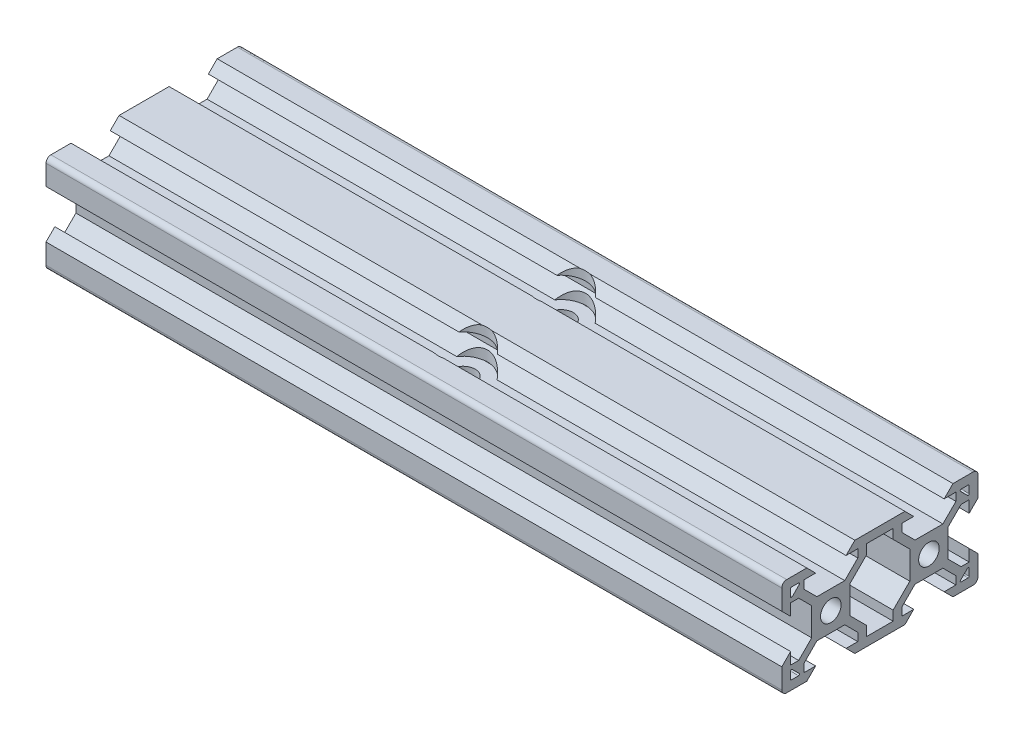
SolidWorks part; units mm, degrees
material "1060 Alloy"
ref_plane "Front Plane" through (0, 0, 0) normal (0, 0, 1) x (1, 0, 0)
ref_plane "Top Plane" through (0, 0, 0) normal (0, 1, 0) x (1, 0, 0)
ref_plane "Right Plane" through (0, 0, 0) normal (1, 0, 0) x (0, 0, -1)
sketch "Sketch4" plane through (0, 0, 0) normal (1, 0, 0) x (0, 0, -1)
  line L0 (-19.2399, 7.0114) -> (20.7601, 7.0114) construction
  dimension "D1" = 40
sketch "Sketch5" plane through (0, 0, 0) normal (1, 0, 0) x (0, 0, -1)
  line L0 (-19.998, 4.9) -> (-18.198, 3.1)
  line L1 (-18.198, 3.1) -> (-18.198, 5.4993)
  line L2 (-18.198, 5.4993) -> (-16.558, 5.4993)
  line L3 (-16.558, 5.4993) -> (-13.9, 2.8413)
  line L4 (-13.9, 2.8413) -> (-13.9, -2.8387)
  line L5 (-13.9, -2.8387) -> (-16.558, -5.4967)
  line L6 (-16.558, -5.4967) -> (-18.198, -5.4967)
  line L7 (-18.198, -5.4967) -> (-18.198, -3.1)
  line L8 (-18.198, -3.1) -> (-19.998, -4.9)
  line L9 (-19.998, -4.9) -> (-19.998, -9)
  line L10 (-18.998, -10) -> (-14.9, -10)
  line L11 (-14.9, -10) -> (-13.1, -8.2)
  line L12 (-13.1, -8.2) -> (-15.5, -8.2)
  line L13 (-15.5, -8.2) -> (-15.5, -6.56)
  line L14 (-15.5, -6.56) -> (-12.84, -3.9)
  line L15 (-12.84, -3.9) -> (-7.16, -3.9)
  line L16 (-7.16, -3.9) -> (-4.5, -6.56)
  line L17 (-4.5, -6.56) -> (-4.5, -8.2)
  line L18 (-4.5, -8.2) -> (-6.9, -8.2)
  line L19 (-6.9, -8.2) -> (-5.1, -10)
  line L20 (-5.1, -10) -> (5.1, -10)
  line L21 (5.1, -10) -> (6.9, -8.2)
  line L22 (6.9, -8.2) -> (4.496, -8.2)
  line L23 (4.496, -8.2) -> (4.496, -6.56)
  line L24 (4.496, -6.56) -> (7.156, -3.9)
  line L25 (7.156, -3.9) -> (12.836, -3.9)
  line L26 (12.836, -3.9) -> (15.496, -6.56)
  line L27 (15.496, -6.56) -> (15.496, -8.2)
  line L28 (15.496, -8.2) -> (13.1, -8.2)
  line L29 (13.1, -8.2) -> (14.9, -10)
  line L30 (14.9, -10) -> (19.002, -10)
  line L31 (20.002, -9) -> (20.002, -4.9)
  line L32 (20.002, -4.9) -> (18.202, -3.1)
  line L33 (18.202, -3.1) -> (18.202, -5.5046)
  line L34 (18.202, -5.5046) -> (16.562, -5.5046)
  line L35 (16.562, -5.5046) -> (13.9, -2.8426)
  line L36 (13.9, -2.8426) -> (13.9, 2.8374)
  line L37 (13.9, 2.8374) -> (16.562, 5.4993)
  line L38 (16.562, 5.4993) -> (18.202, 5.4993)
  line L39 (18.202, 5.4993) -> (18.202, 3.1)
  line L40 (18.202, 3.1) -> (20.002, 4.9)
  line L41 (20.002, 4.9) -> (20.002, 9)
  line L42 (19.002, 10) -> (14.9, 10)
  line L43 (14.9, 10) -> (13.1, 8.2)
  line L44 (13.1, 8.2) -> (15.5013, 8.2)
  line L45 (15.5013, 8.2) -> (15.5013, 6.56)
  line L46 (15.5013, 6.56) -> (12.8413, 3.9)
  line L47 (12.8413, 3.9) -> (7.1613, 3.9)
  line L48 (7.1613, 3.9) -> (4.5013, 6.56)
  line L49 (4.5013, 6.56) -> (4.5013, 8.2)
  line L50 (4.5013, 8.2) -> (6.9, 8.2)
  line L51 (6.9, 8.2) -> (5.1, 10)
  line L52 (5.1, 10) -> (-5.1, 10)
  line L53 (-5.1, 10) -> (-6.9, 8.2)
  line L54 (-6.9, 8.2) -> (-4.5013, 8.2)
  line L55 (-4.5013, 8.2) -> (-4.5013, 6.56)
  line L56 (-4.5013, 6.56) -> (-7.1613, 3.9)
  line L57 (-7.1613, 3.9) -> (-12.8413, 3.9)
  line L58 (-12.8413, 3.9) -> (-15.5013, 6.56)
  line L59 (-15.5013, 6.56) -> (-15.5013, 8.2)
  line L60 (-15.5013, 8.2) -> (-13.1, 8.2)
  line L61 (-13.1, 8.2) -> (-14.9, 10)
  line L62 (-14.9, 10) -> (-18.998, 10)
  line L63 (-19.998, 9) -> (-19.998, 4.9)
  line L64 (6.1, -2.84) -> (6.1, 2.84)
  line L65 (6.1, 2.84) -> (2.7, 6.24)
  line L66 (2.7, 6.24) -> (2.7, 8.2)
  line L67 (2.7, 8.2) -> (-2.7, 8.2)
  line L68 (-2.7, 8.2) -> (-2.7, 6.24)
  line L69 (-2.7, 6.24) -> (-6.1, 2.84)
  line L70 (-6.1, 2.84) -> (-6.1, -2.84)
  line L71 (-6.1, -2.84) -> (-2.7, -6.24)
  line L72 (-2.7, -6.24) -> (-2.7, -8.2)
  line L73 (-2.7, -8.2) -> (2.7, -8.2)
  line L74 (2.7, -8.2) -> (2.7, -6.24)
  line L75 (2.7, -6.24) -> (6.1, -2.84)
  line L76 (0, -8.2) -> (0, 8.2) construction
  line L77 (6.1, 0) -> (-6.1, 0) construction
  line L78 (16.562, 5.4993) -> (15.5013, 6.56) construction
  line L79 (16.5713, 8.2) -> (18.002, 8.2)
  line L81 (17.8606, 6.4279) -> (16.4299, 7.8586)
  line L82 (18.202, 8) -> (18.202, 6.5693)
  line L83 (18.002, 6.5693) -> (18.002, 8) construction
  line L84 (18.002, 8) -> (16.5713, 8) construction
  line L85 (16.5713, 8) -> (18.002, 6.5693) construction
  line L86 (16.5713, -8.2) -> (18.002, -8.2)
  line L87 (18.202, -8) -> (18.202, -6.5693)
  line L88 (17.8606, -6.4279) -> (16.4299, -7.8586)
  line L89 (-17.8606, 6.4279) -> (-16.4299, 7.8586)
  line L90 (-16.5713, 8.2) -> (-18.002, 8.2)
  line L91 (-18.202, 8) -> (-18.202, 6.5693)
  line L92 (-16.5713, -8.2) -> (-18.002, -8.2)
  line L93 (-17.8606, -6.4279) -> (-16.4299, -7.8586)
  line L94 (-18.202, -8) -> (-18.202, -6.5693)
  circle A0 centre (-10, 0) radius 2.1
  circle A1 centre (10, 0) radius 2.1
  arc A2 (-19.998, -9) -> (-18.998, -10) centre (-18.998, -9) ccw
  arc A5 (-18.998, 10) -> (-19.998, 9) centre (-18.998, 9) ccw
  arc A6 (20.002, -9) -> (19.002, -10) centre (19.002, -9) cw
  arc A7 (20.002, 9) -> (19.002, 10) centre (19.002, 9) ccw
  arc A8 (18.002, 8.2) -> (18.202, 8) centre (18.002, 8) cw
  arc A10 (16.4299, 7.8586) -> (16.5713, 8.2) centre (16.5713, 8) cw
  arc A12 (18.202, 6.5693) -> (17.8606, 6.4279) centre (18.002, 6.5693) cw
  arc A13 (16.4299, -7.8586) -> (16.5713, -8.2) centre (16.5713, -8) ccw
  arc A14 (18.002, -8.2) -> (18.202, -8) centre (18.002, -8) ccw
  arc A15 (18.202, -6.5693) -> (17.8606, -6.4279) centre (18.002, -6.5693) ccw
  arc A16 (-18.202, 6.5693) -> (-17.8606, 6.4279) centre (-18.002, 6.5693) ccw
  arc A17 (-16.4299, 7.8586) -> (-16.5713, 8.2) centre (-16.5713, 8) ccw
  arc A18 (-18.002, 8.2) -> (-18.202, 8) centre (-18.002, 8) ccw
  arc A19 (-18.002, -8.2) -> (-18.202, -8) centre (-18.002, -8) cw
  arc A20 (-16.4299, -7.8586) -> (-16.5713, -8.2) centre (-16.5713, -8) cw
  arc A21 (-18.202, -6.5693) -> (-17.8606, -6.4279) centre (-18.002, -6.5693) cw
  dimension "D1" = 4.2
  dimension "D20" = 3.9
  dimension "D27" = 1
  dimension "D40" = 1
  dimension "D41" = 1
  dimension "D42" = 1
  dimension "D45" = 0.2
  dimension "D47" = 1.07
  dimension "D48" = 1.07
  dimension "D49" = 0.2
  dimension "D2" = 20
  dimension "D3" = 10
  dimension "D4" = 5.68
  dimension "D5" = 5.4
  dimension "D6" = 1.96
  dimension "D7" = 45
  dimension "D8" = 1.8
  dimension "D9" = 1.64
  dimension "D10" = 1.8
  dimension "D11" = 40
  dimension "D12" = 20
  dimension "D13" = 3.9
  dimension "D14" = 1.5
  dimension "D15" = 1.5
  dimension "D16" = 3.9
  dimension "D17" = 3.9
  dimension "D18" = 3.9
  dimension "D19" = 3.9
  dimension "D21" = 1.5
  dimension "D22" = 1.5
  dimension "D23" = 1.64
  dimension "D24" = 45
  dimension "D25" = 1.5
  dimension "D26" = 1.8
  dimension "D28" = 6.2
  dimension "D29" = 6.2
  dimension "D30" = 6.2
  dimension "D31" = 6.2
  dimension "D32" = 6.2
  dimension "D33" = 3.1
  dimension "D34" = 3.1
  dimension "D35" = 3.1
  dimension "D36" = 3.1
  dimension "D37" = 6.2
  dimension "D38" = 3.1
  dimension "D39" = 3.1
  dimension "D43" = 1.64
  dimension "D44" = 135
  dimension "D46" = 45
extrude "Boss-Extrude1" add sketch "Sketch5" along normal mid plane 150
sketch "Sketch6" plane through (0, 10, 0) normal (0, 1, 0) x (1, 0, 0)
  line L0 (75, 10.0013) -> (-75, 10.0013) construction
  line L3 (75, 12.8413) -> (75, 7.1613) construction
  line L4 (-75, 12.8413) -> (-75, 7.1613) construction
  line L5 (0, 10.0013) -> (0, -18.998) construction
  line L6 (75, -18.998) -> (-75, -18.998) construction
  line L7 (-75, 0) -> (75, 0) construction
  line L8 (-75, 5.1) -> (-75, -5.1) construction
  line L9 (75, 5.1) -> (75, -5.1) construction
  circle A0 centre (0, 10.0013) radius 2.5
  circle A1 centre (0, -10.0013) radius 2.5
  dimension "D1" = 5
extrude "Cut-Extrude1" cut sketch "Sketch6" against normal up to next
sketch "Sketch7" plane through (0, 10, 0) normal (0, 1, 0) x (1, 0, 0)
  line L0 (-75, 0) -> (75, 0) construction
  line L1 (-75, 5.1) -> (-75, -5.1) construction
  line L2 (75, 5.1) -> (75, -5.1) construction
  circle A0 centre (0, 10.0013) radius 5
  circle A1 centre (0, -10.0013) radius 5
  dimension "D1" = 10
extrude "Cut-Extrude2" cut sketch "Sketch7" against normal up to surface (6.1 mm away) up to face at (0, 3.9, -12.5013)
